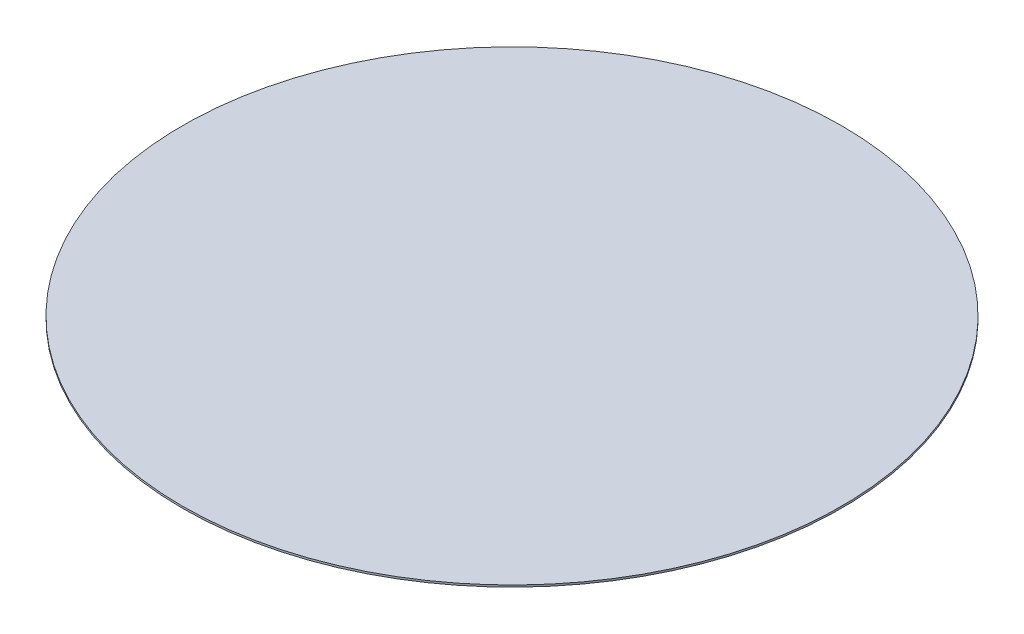
SolidWorks part; units mm, degrees
ref_plane "Front Plane" through (0, 0, 0) normal (0, 0, 1) x (1, 0, 0)
ref_plane "Top Plane" through (0, 0, 0) normal (0, 1, 0) x (1, 0, 0)
ref_plane "Right Plane" through (0, 0, 0) normal (1, 0, 0) x (0, 0, -1)
sketch "Sketch1" plane through (0, 0, 0) normal (0, 1, 0) x (1, 0, 0)
  circle A0 centre (0, 0) radius 175
  dimension "D1" = 350
extrude "Boss-Extrude1" add sketch "Sketch1" along normal blind 1
